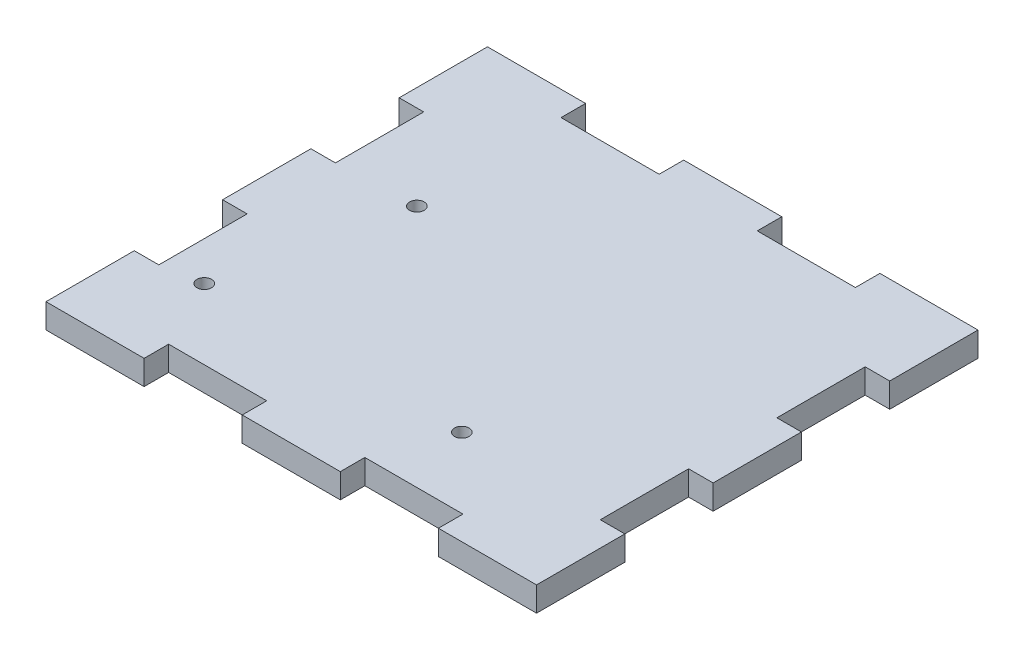
SolidWorks part; units mm, degrees
ref_plane "Front Plane" through (0, 0, 0) normal (0, 0, 1) x (1, 0, 0)
ref_plane "Top Plane" through (0, 0, 0) normal (0, 1, 0) x (1, 0, 0)
ref_plane "Right Plane" through (0, 0, 0) normal (1, 0, 0) x (0, 0, -1)
sketch "Sketch1" plane through (0, 0, 0) normal (0, 1, 0) x (1, 0, 0)
  line L1 (-63.5, -57.15) -> (63.5, -57.15)
  line L2 (-63.5, -57.15) -> (-63.5, 57.15)
  line L3 (-63.5, 57.15) -> (63.5, 57.15)
  line L4 (63.5, -57.15) -> (63.5, 57.15)
  line L5 (-63.5, -57.15) -> (63.5, 57.15) construction
  line L6 (-63.5, 57.15) -> (63.5, -57.15) construction
  point P0 (0, 0)
  dimension "D1" = 114.3
  dimension "D2" = 127
extrude "Boss-Extrude1" add sketch "Sketch1" along normal blind 6.35
sketch "Sketch2" plane through (0, 6.35, 0) normal (0, 1, 0) x (1, 0, 0)
  line L0 (-63.5, 57.15) -> (-63.5, -57.15) construction
  line L1 (-63.5, -34.29) -> (-57.15, -34.29)
  line L2 (-63.5, -34.29) -> (-63.5, -11.43)
  line L3 (-63.5, -11.43) -> (-57.15, -11.43)
  line L4 (-57.15, -34.29) -> (-57.15, -11.43)
  line L5 (63.5, 57.15) -> (-63.5, 57.15) construction
  line L6 (-63.5, 11.43) -> (-57.15, 11.43)
  line L7 (-63.5, 11.43) -> (-63.5, 34.29)
  line L8 (-63.5, 34.29) -> (-57.15, 34.29)
  line L9 (-57.15, 11.43) -> (-57.15, 34.29)
  line L10 (-38.1, 57.15) -> (-12.7, 57.15)
  line L11 (-38.1, 57.15) -> (-38.1, 50.8)
  line L12 (-38.1, 50.8) -> (-12.7, 50.8)
  line L13 (-12.7, 57.15) -> (-12.7, 50.8)
  line L14 (0, 0) -> (0, 57.15) construction
  line L15 (12.7, 57.15) -> (38.1, 57.15)
  line L16 (12.7, 57.15) -> (12.7, 50.8)
  line L17 (12.7, 50.8) -> (38.1, 50.8)
  line L18 (38.1, 57.15) -> (38.1, 50.8)
  line L19 (0, 0) -> (63.5, 0) construction
  line L20 (63.5, -57.15) -> (63.5, 57.15) construction
  line L21 (-57.15, 34.29) -> (-57.15, 57.15) construction
  line L22 (-57.15, 11.43) -> (-57.15, -11.43) construction
  line L23 (-57.15, -34.29) -> (-57.15, -57.15) construction
  line L24 (-63.5, -57.15) -> (63.5, -57.15) construction
  line L25 (-38.1, 50.8) -> (-63.5, 50.8) construction
  line L26 (-12.7, 50.8) -> (12.7, 50.8) construction
  line L27 (38.1, 50.8) -> (63.5, 50.8) construction
  line L28 (57.15, -34.29) -> (57.15, -57.15) construction
  line L29 (57.15, 11.43) -> (57.15, -11.43) construction
  line L30 (57.15, 34.29) -> (57.15, 57.15) construction
  line L31 (57.15, 11.43) -> (57.15, 34.29)
  line L32 (63.5, 34.29) -> (57.15, 34.29)
  line L33 (63.5, 11.43) -> (63.5, 34.29)
  line L34 (63.5, 11.43) -> (57.15, 11.43)
  line L35 (57.15, -34.29) -> (57.15, -11.43)
  line L36 (63.5, -11.43) -> (57.15, -11.43)
  line L37 (63.5, -34.29) -> (63.5, -11.43)
  line L38 (63.5, -34.29) -> (57.15, -34.29)
  line L39 (38.1, -50.8) -> (63.5, -50.8) construction
  line L40 (-12.7, -50.8) -> (12.7, -50.8) construction
  line L41 (-38.1, -50.8) -> (-63.5, -50.8) construction
  line L42 (38.1, -57.15) -> (38.1, -50.8)
  line L43 (12.7, -50.8) -> (38.1, -50.8)
  line L44 (12.7, -57.15) -> (12.7, -50.8)
  line L45 (12.7, -57.15) -> (38.1, -57.15)
  line L46 (-12.7, -57.15) -> (-12.7, -50.8)
  line L47 (-38.1, -50.8) -> (-12.7, -50.8)
  line L48 (-38.1, -57.15) -> (-38.1, -50.8)
  line L49 (-38.1, -57.15) -> (-12.7, -57.15)
extrude "Cut-Extrude1" cut sketch "Sketch2" against normal through all
sketch "Sketch3" plane through (0, 6.35, 0) normal (0, 1, 0) x (1, 0, 0)
  circle A0 centre (-47.0763, -32.6007) radius 1.8986 construction
  circle A1 centre (19.5987, -32.6007) radius 1.8986 construction
  circle A2 centre (-47.0763, -32.6007) radius 1.8986
  circle A3 centre (19.5987, -32.6007) radius 1.8986
extrude "Cut-Extrude2" cut sketch "Sketch3" against normal through all
sketch "Sketch4" plane through (0, 0, 0) normal (0, -1, 0) x (1, 0, 0)
  circle A0 centre (-36.9163, -12.2807) radius 1.8986 construction
  circle A1 centre (-36.9163, -12.2807) radius 1.8986
extrude "Cut-Extrude3" cut sketch "Sketch4" against normal through all
equation "\"D1@Boss-Extrude1\" = \"material\""
equation "\"material\"=\"GMaterial@Platform.assembly\""
